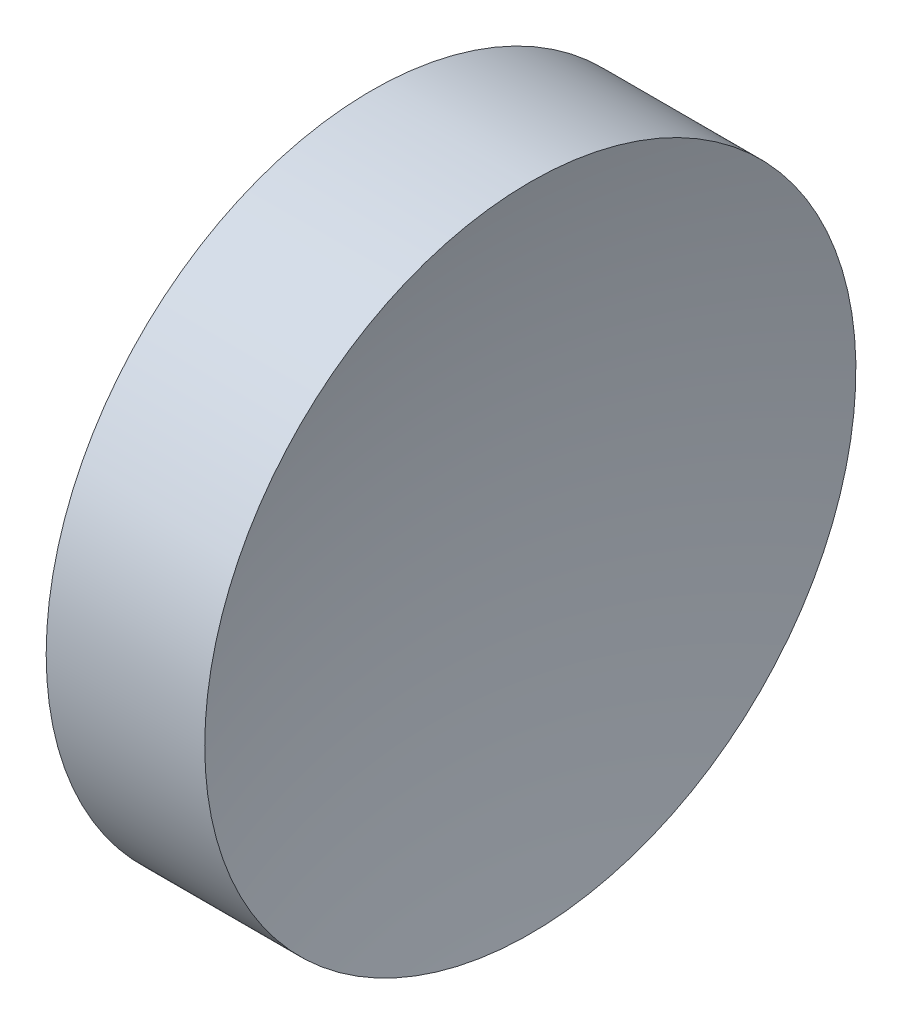
SolidWorks part; units mm, degrees
ref_plane "前视基准面" through (0, 0, 0) normal (0, 0, 1) x (1, 0, 0)
ref_plane "上视基准面" through (0, 0, 0) normal (0, 1, 0) x (1, 0, 0)
ref_plane "右视基准面" through (0, 0, 0) normal (1, 0, 0) x (0, 0, -1)
sketch "草图1" plane through (0, 0, 0) normal (0, 0, 1) x (1, 0, 0)
  line L0 (217.9703, 138.756) -> (265.5527, 138.756) construction
  line L1 (230.1853, 138.756) -> (230.1853, 163.756)
  line L2 (239.1853, 138.756) -> (230.1853, 138.756)
  line L3 (230.1853, 163.756) -> (242.3607, 163.756)
  arc A0 (242.3607, 163.756) -> (239.1853, 138.756) centre (339.1853, 138.756) ccw
  dimension "D1" = 100
  dimension "D2" = 12.1754
  dimension "D3" = 25
revolve "旋转1" add sketch "草图1" angle 360 about L0
